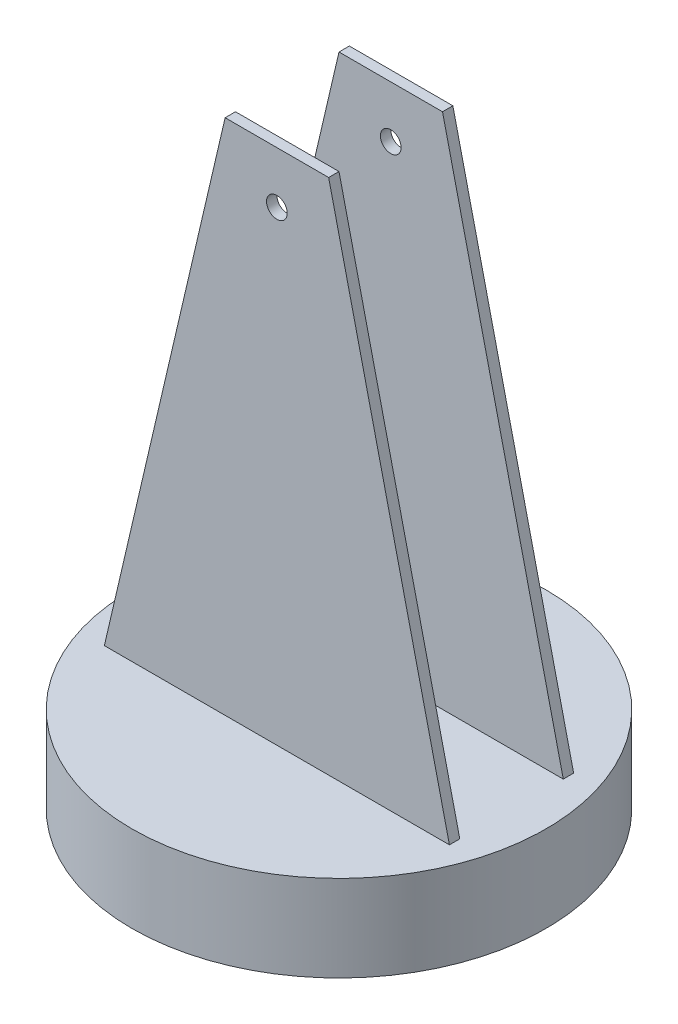
SolidWorks part; units mm, degrees
material "Teca"
ref_plane "Alzado" through (0, 0, 0) normal (0, 0, 1) x (1, 0, 0)
ref_plane "Planta" through (0, 0, 0) normal (0, 1, 0) x (1, 0, 0)
ref_plane "Vista lateral" through (0, 0, 0) normal (1, 0, 0) x (0, 0, -1)
sketch "Croquis1" plane through (0, 0, 0) normal (0, 1, 0) x (1, 0, 0)
  circle A0 centre (0, 0) radius 60
extrude "Saliente-Extruir3" add sketch "Croquis1" along normal blind 25
ref_plane "Plano3" through (0, 25, 0) normal (0, 1, 0) x (1, 0, 0)
sketch "Croquis4" plane through (0, 25, 0) normal (0, 1, 0) x (1, 0, 0)
  line L0 (0, 0) -> (60, 0) construction
  line L1 (0, 0) -> (-60, 0) construction
  line L2 (-50, 15) -> (50, 15)
  line L4 (0, -15) -> (50, -15)
  line L5 (50, 15) -> (50, 18)
  line L6 (50, 18) -> (-50, 18)
  line L7 (-50, 18) -> (-50, 15)
  line L8 (50, -15) -> (50, -18)
  line L9 (50, -18) -> (-50, -18)
  line L10 (-50, -18) -> (-50, -15)
  line L11 (-50, -15) -> (0, -15)
  circle A0 centre (0, 0) radius 60 construction
extrude "Saliente-Extruir5" add sketch "Croquis4" along normal blind 150
ref_plane "Plano5" through (0, 0, 18) normal (0, 0, 1) x (1, 0, 0)
sketch "Croquis10" plane through (0, 0, 18) normal (0, 0, 1) x (1, 0, 0)
  line L0 (0, 175) -> (15, 175)
  line L1 (-50, 175) -> (50, 175) construction
  line L2 (0, 175) -> (-15, 175) construction
  line L3 (-15, 175) -> (-50, 25)
  line L4 (-50, 25) -> (-50, 175)
  line L5 (-50, 175) -> (-15, 175)
  line L6 (0, 175) -> (15, 175) construction
  line L7 (15, 175) -> (50, 175)
  line L8 (50, 175) -> (50, 25)
  line L9 (50, 25) -> (15, 175)
  line L10 (-15, 175) -> (-50, 175)
  line L11 (15, 175) -> (50, 175)
extrude "Cortar-Extruir3" cut sketch "Croquis10" against normal blind 150 contours L5 L4 L3 | L9 L8 L7
sketch "Croquis11" plane through (0, 0, 18) normal (0, 0, 1) x (1, 0, 0)
  line L0 (0, 175) -> (0, 160) construction
  line L1 (-15, 175) -> (15, 175) construction
  circle A0 centre (0, 160) radius 3
extrude "Cortar-Extruir4" cut sketch "Croquis11" against normal blind 150
